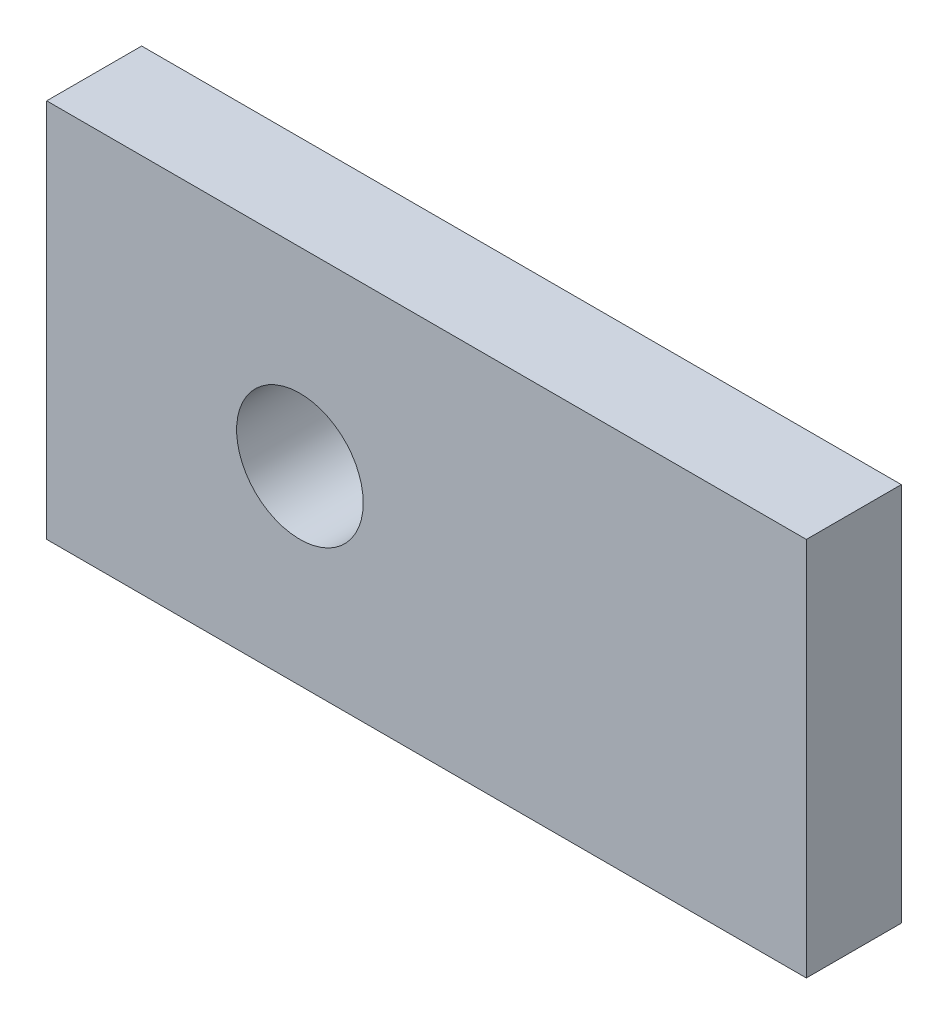
SolidWorks part; units mm, degrees
ref_plane "Plan de face" through (0, 0, 0) normal (0, 0, 1) x (1, 0, 0)
ref_plane "Plan de dessus" through (0, 0, 0) normal (0, 1, 0) x (1, 0, 0)
ref_plane "Plan de droite" through (0, 0, 0) normal (1, 0, 0) x (0, 0, -1)
sketch "Esquisse1" plane through (0, 0, 0) normal (0, 0, 1) x (1, 0, 0)
  line L0 (-60, 0) -> (60, 0)
other "Elément mécano-soudé1"
ref_plane "Plan1" through (-60, 0, 0) normal (1, 0, 0) x (0, 1, 0)
sketch "plat" plane through (-60, 0, 0) normal (1, 0, 0) x (0, 1, 0)
  line L0 (-30, 0) -> (30, 0) construction
  line L1 (-30, 7.5) -> (30, 7.5)
  line L2 (-30, 7.5) -> (-30, -7.5)
  line L3 (-30, -7.5) -> (30, -7.5)
  line L4 (30, 7.5) -> (30, -7.5)
  line L5 (0, 7.5) -> (0, -7.5) construction
  point P8 (0, 0)
  dimension "B" = 60
  dimension "A" = 15
sketch "Esquisse2" plane through (0, 0, 7.5) normal (0, 0, 1) x (1, 0, 0)
  line L0 (-60, 0) -> (60, 0) construction
  line L1 (60, 30) -> (60, -30) construction
  circle A0 centre (-20, 0) radius 10
  dimension "D1" = 20
  dimension "D2" = 80
extrude "Enlèv. mat.-Extru.1" cut sketch "Esquisse2" against normal blind 20
